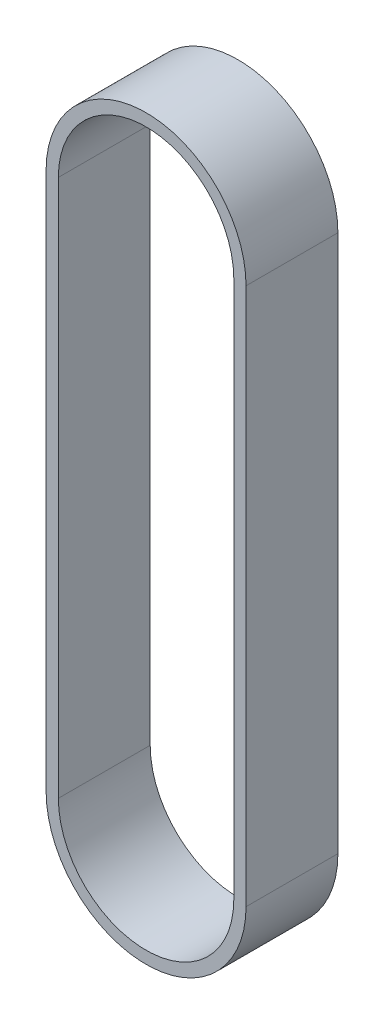
SolidWorks part; units mm, degrees
material "普通碳钢"
ref_plane "前视基准面" through (0, 0, 0) normal (0, 0, 1) x (1, 0, 0)
ref_plane "上视基准面" through (0, 0, 0) normal (0, 1, 0) x (1, 0, 0)
ref_plane "右视基准面" through (0, 0, 0) normal (1, 0, 0) x (0, 0, -1)
sketch "草图1" plane through (0, 0, 0) normal (0, 0, 1) x (1, 0, 0)
  line L0 (0, 0) -> (0, -87.8) construction
  line L1 (14.325, 0) -> (14.325, -87.8)
  line L2 (-14.325, 0) -> (-14.325, -87.8)
  arc A0 (14.325, 0) -> (-14.325, 0) centre (0, 0) ccw
  arc A1 (-14.325, -87.8) -> (14.325, -87.8) centre (0, -87.8) ccw
  point P3 (0, -43.9)
  dimension "D1" = 87.8
  dimension "D2" = 28.65
extrude "拉伸-薄壁1" add sketch "草图1" along normal mid plane 15 thin thin type one direction wall 2
